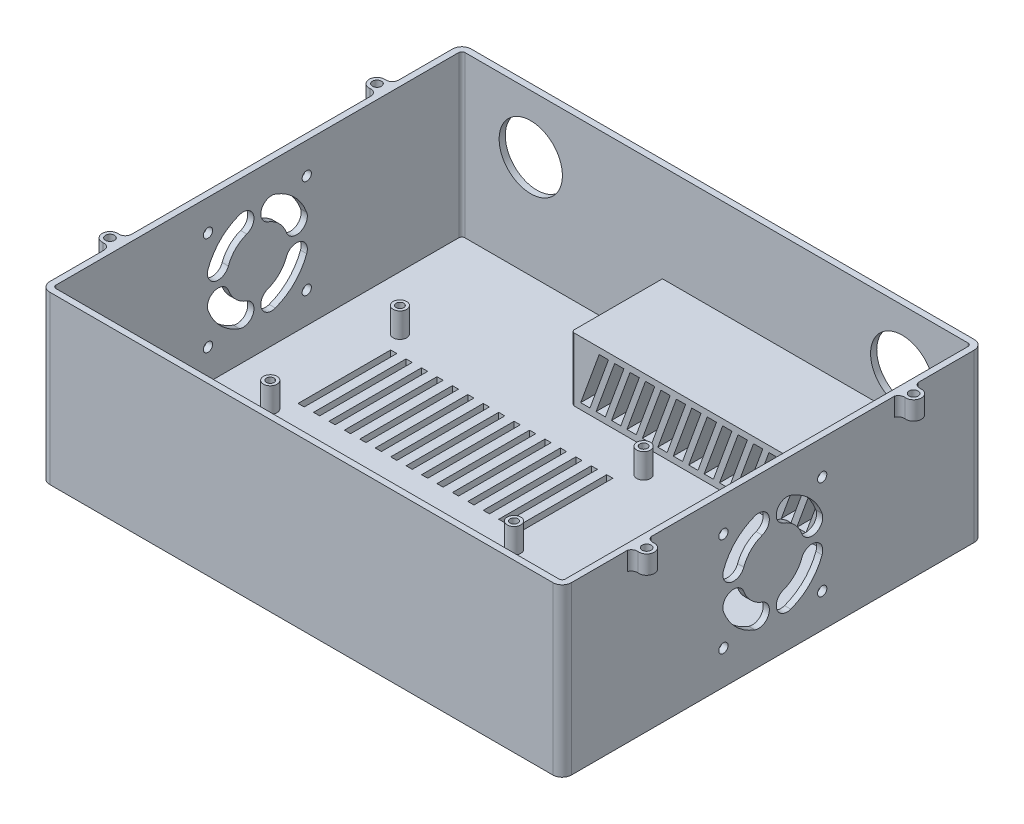
SolidWorks part; units mm, degrees
ref_plane "前视基准面" through (0, 0, 0) normal (0, 0, 1) x (1, 0, 0)
ref_plane "上视基准面" through (0, 0, 0) normal (0, 1, 0) x (1, 0, 0)
ref_plane "右视基准面" through (0, 0, 0) normal (1, 0, 0) x (0, 0, -1)
sketch "草图2" plane through (0, 0, 0) normal (0, 1, 0) x (1, 0, 0)
  line L0 (-81.5, -68.25) -> (81.5, -68.25)
  line L1 (-81.5, -66.25) -> (81.5, -66.25)
  line L2 (-82.5, -65.25) -> (-82.5, 65.25)
  line L3 (-81.5, 66.25) -> (81.5, 66.25)
  line L4 (82.5, -65.25) -> (82.5, 65.25)
  line L5 (-82.5, -66.25) -> (82.5, 66.25) construction
  line L6 (-82.5, 66.25) -> (82.5, -66.25) construction
  line L7 (84.5, -65.25) -> (84.5, 65.25)
  line L8 (-81.5, 68.25) -> (81.5, 68.25)
  line L9 (-84.5, -65.25) -> (-84.5, 65.25)
  arc A0 (-81.5, -66.25) -> (-82.5, -65.25) centre (-81.5, -65.25) cw
  arc A1 (81.5, -66.25) -> (82.5, -65.25) centre (81.5, -65.25) ccw
  arc A2 (81.5, 66.25) -> (82.5, 65.25) centre (81.5, 65.25) cw
  arc A3 (-82.5, 65.25) -> (-81.5, 66.25) centre (-81.5, 65.25) cw
  arc A4 (81.5, -68.25) -> (84.5, -65.25) centre (81.5, -65.25) ccw
  arc A5 (81.5, 68.25) -> (84.5, 65.25) centre (81.5, 65.25) cw
  arc A6 (-84.5, 65.25) -> (-81.5, 68.25) centre (-81.5, 65.25) cw
  arc A7 (-81.5, -68.25) -> (-84.5, -65.25) centre (-81.5, -65.25) cw
  point P0 (0, 0)
  dimension "D3" = 1
  dimension "D1" = 132.5
  dimension "D2" = 165
  dimension "D4" = 2
extrude "凸台-拉伸4" add sketch "草图2" along normal blind 52
sketch "草图6" plane through (0, 0, 0) normal (0, -1, 0) x (-1, 0, 0)
  line L0 (-84.5, -65.25) -> (-84.5, 65.25) construction
  line L1 (81.5, -68.25) -> (-81.5, -68.25)
  line L2 (84.5, -65.25) -> (84.5, 65.25)
  line L3 (81.5, 68.25) -> (-81.5, 68.25)
  line L4 (-84.5, -65.25) -> (-84.5, 65.25)
  line L5 (-81.5, 68.25) -> (81.5, 68.25) construction
  line L6 (84.5, 65.25) -> (84.5, -65.25) construction
  line L7 (81.5, -68.25) -> (-81.5, -68.25) construction
  arc A0 (84.5, 65.25) -> (81.5, 68.25) centre (81.5, 65.25) ccw
  arc A1 (-81.5, 68.25) -> (-84.5, 65.25) centre (-81.5, 65.25) ccw
  arc A2 (-81.5, -68.25) -> (-84.5, -65.25) centre (-81.5, -65.25) cw
  arc A3 (81.5, -68.25) -> (84.5, -65.25) centre (81.5, -65.25) ccw
  dimension "D1" = 3
extrude "凸台-拉伸5" add sketch "草图6" along normal blind 2
sketch "草图7" plane through (0, 0, 0) normal (0, 1, 0) x (1, 0, 0)
  line L0 (82.5, -65.25) -> (82.5, 65.25) construction
  line L1 (-17.5, 66.25) -> (82.5, 66.25)
  line L2 (-17.5, 66.25) -> (-17.5, 37.75)
  line L3 (-16.5, 36.75) -> (82.5, 36.75)
  line L4 (82.5, 66.25) -> (82.5, 36.75)
  line L5 (81.5, 66.25) -> (-81.5, 66.25) construction
  arc A0 (-17.5, 37.75) -> (-16.5, 36.75) centre (-16.5, 37.75) ccw
  dimension "D1" = 1
  dimension "D2" = 29.5
  dimension "D3" = 100
extrude "凸台-拉伸6" add sketch "草图7" along normal blind 20.5
sketch "草图14" plane through (0, 0, -68.25) normal (0, 0, -1) x (-1, 0, 0)
  line L0 (0, 68.0552) -> (0, -20.1573) construction
  line L1 (-81.5, 52) -> (81.5, 52) construction
  circle A0 centre (-60.175, 33.275) radius 10.25
  circle A1 centre (60.175, 33.275) radius 10.25
  dimension "D1" = 20.5
  dimension "D2" = 120.35
  dimension "D3" = 18.725
extrude "切除-拉伸2" cut sketch "草图14" against normal blind 2
sketch "草图20" plane through (0, 0, -36.75) normal (0, 0, 1) x (1, 0, 0)
  line L0 (-14.5, 2) -> (-8.4945, 18.5)
  line L1 (-14.5, 2) -> (-11.5, 2)
  line L2 (-8.4945, 18.5) -> (-5.4945, 18.5)
  line L3 (-11.5, 2) -> (-5.4945, 18.5)
  line L4 (-16.5, 0) -> (82.5, 0) construction
  line L5 (-16.5, 20.5) -> (-16.5, 0) construction
  line L6 (-16.5, 20.5) -> (82.5, 20.5) construction
  line L7 (-9.5, 2) -> (-3.4945, 18.5)
  line L8 (-3.4945, 18.5) -> (-0.4945, 18.5)
  line L9 (-6.5, 2) -> (-0.4945, 18.5)
  line L10 (-9.5, 2) -> (-6.5, 2)
  line L11 (-4.5, 2) -> (1.5055, 18.5)
  line L12 (1.5055, 18.5) -> (4.5055, 18.5)
  line L13 (-1.5, 2) -> (4.5055, 18.5)
  line L14 (-4.5, 2) -> (-1.5, 2)
  line L15 (0.5, 2) -> (6.5055, 18.5)
  line L16 (6.5055, 18.5) -> (9.5055, 18.5)
  line L17 (3.5, 2) -> (9.5055, 18.5)
  line L18 (0.5, 2) -> (3.5, 2)
  line L19 (5.5, 2) -> (11.5055, 18.5)
  line L20 (11.5055, 18.5) -> (14.5055, 18.5)
  line L21 (8.5, 2) -> (14.5055, 18.5)
  line L22 (5.5, 2) -> (8.5, 2)
  line L23 (10.5, 2) -> (16.5055, 18.5)
  line L24 (16.5055, 18.5) -> (19.5055, 18.5)
  line L25 (13.5, 2) -> (19.5055, 18.5)
  line L26 (10.5, 2) -> (13.5, 2)
  line L27 (15.5, 2) -> (21.5055, 18.5)
  line L28 (21.5055, 18.5) -> (24.5055, 18.5)
  line L29 (18.5, 2) -> (24.5055, 18.5)
  line L30 (15.5, 2) -> (18.5, 2)
  line L31 (20.5, 2) -> (26.5055, 18.5)
  line L32 (26.5055, 18.5) -> (29.5055, 18.5)
  line L33 (23.5, 2) -> (29.5055, 18.5)
  line L34 (20.5, 2) -> (23.5, 2)
  line L35 (25.5, 2) -> (31.5055, 18.5)
  line L36 (31.5055, 18.5) -> (34.5055, 18.5)
  line L37 (28.5, 2) -> (34.5055, 18.5)
  line L38 (25.5, 2) -> (28.5, 2)
  line L39 (30.5, 2) -> (36.5055, 18.5)
  line L40 (36.5055, 18.5) -> (39.5055, 18.5)
  line L41 (33.5, 2) -> (39.5055, 18.5)
  line L42 (30.5, 2) -> (33.5, 2)
  line L43 (35.5, 2) -> (41.5055, 18.5)
  line L44 (41.5055, 18.5) -> (44.5055, 18.5)
  line L45 (38.5, 2) -> (44.5055, 18.5)
  line L46 (35.5, 2) -> (38.5, 2)
  line L47 (40.5, 2) -> (46.5055, 18.5)
  line L48 (46.5055, 18.5) -> (49.5055, 18.5)
  line L49 (43.5, 2) -> (49.5055, 18.5)
  line L50 (40.5, 2) -> (43.5, 2)
  line L51 (45.5, 2) -> (51.5055, 18.5)
  line L52 (51.5055, 18.5) -> (54.5055, 18.5)
  line L53 (48.5, 2) -> (54.5055, 18.5)
  line L54 (45.5, 2) -> (48.5, 2)
  line L55 (50.5, 2) -> (56.5055, 18.5)
  line L56 (56.5055, 18.5) -> (59.5055, 18.5)
  line L57 (53.5, 2) -> (59.5055, 18.5)
  line L58 (50.5, 2) -> (53.5, 2)
  line L59 (55.5, 2) -> (61.5055, 18.5)
  line L60 (61.5055, 18.5) -> (64.5055, 18.5)
  line L61 (58.5, 2) -> (64.5055, 18.5)
  line L62 (55.5, 2) -> (58.5, 2)
  line L63 (60.5, 2) -> (66.5055, 18.5)
  line L64 (66.5055, 18.5) -> (69.5055, 18.5)
  line L65 (63.5, 2) -> (69.5055, 18.5)
  line L66 (60.5, 2) -> (63.5, 2)
  line L67 (65.5, 2) -> (71.5055, 18.5)
  line L68 (71.5055, 18.5) -> (74.5055, 18.5)
  line L69 (68.5, 2) -> (74.5055, 18.5)
  line L70 (65.5, 2) -> (68.5, 2)
  line L71 (70.5, 2) -> (76.5055, 18.5)
  line L72 (76.5055, 18.5) -> (79.5055, 18.5)
  line L73 (73.5, 2) -> (79.5055, 18.5)
  line L74 (70.5, 2) -> (73.5, 2)
  line L75 (-14.5, 2) -> (-9.5, 2) construction
  dimension "D1" = 2
  dimension "D2" = 2
  dimension "D3" = 2
  dimension "D4" = 110
  dimension "D5" = 3
  dimension "D7" = 5
  dimension "D6" = 18
sketch "草图21" plane through (0, 0, -36.75) normal (0, 0, 1) x (1, 0, 0)
extrude "切除-拉伸4" cut sketch "草图20" against normal blind 35
sketch "草图22" plane through (0, 0, -68.25) normal (0, 0, -1) x (-1, 0, 0)
  line L1 (81.5, -2) -> (-81.5, -2) construction
  text T0 "<b>GAAS</b>" font "Monospac821 BT" height 16.5
  dimension "D1" = 4
  dimension "D2" = 4
extrude "切除-拉伸5" cut sketch "草图22" against normal blind 0.05
sketch "草图25" plane through (0, 0, 0) normal (0, 1, 0) x (1, 0, 0)
  line L0 (-81.5, -66.25) -> (81.5, -66.25) construction
  line L1 (0, 72.7206) -> (0, -77.048) construction
  circle A0 centre (-60.15, -50.45) radius 10.15
  circle A1 centre (60.15, -50.45) radius 10.15
  dimension "D2" = 20.3
  dimension "D3" = 15.8
  dimension "D1" = 120.3
extrude "切除-拉伸6" cut sketch "草图25" against normal blind 2
sketch "草图26" plane through (0, 0, 0) normal (0, 1, 0) x (1, 0, 0)
  line L0 (-104.0478, -34.75) -> (111.3857, -35.8789) construction
  line L1 (-81.5, -66.25) -> (81.5, -66.25) construction
  line L3 (-16.5, 36.75) -> (82.5, 36.75) construction
  line L10 (-82.5, 65.25) -> (-82.5, -65.25) construction
  circle A0 centre (13.9, 28.75) radius 1.25
  circle A1 centre (13.9, -13.25) radius 1.25
  circle A2 centre (-65.065, -13.25) radius 1.25
  circle A3 centre (-65.065, 28.75) radius 1.25
  circle A4 centre (13.9, 28.75) radius 2.2
  circle A5 centre (13.9, -13.25) radius 2.2
  circle A6 centre (-65.065, -13.25) radius 2.2
  circle A7 centre (-65.065, 28.75) radius 2.2
  dimension "D7" = 8
  dimension "D9" = 2.5
  dimension "D4" = 4.4
  dimension "D1" = 31.5
  dimension "D2" = 71.9578
  dimension "D3" = 96.4
  dimension "D11" = 42
  dimension "D12" = 78.965
extrude "凸台-拉伸13" add sketch "草图26" along normal blind 8
sketch "草图30" plane through (0, 0, 0) normal (0, 1, 0) x (1, 0, 0)
  line L0 (-65.065, 28.75) -> (-65.065, -13.25) construction
  line L1 (-62.065, 22.75) -> (-60.065, 22.75)
  line L2 (-62.065, 22.75) -> (-62.065, -7.25)
  line L3 (-62.065, -7.25) -> (-60.065, -7.25)
  line L4 (-60.065, 22.75) -> (-60.065, -7.25)
  line L5 (-57.065, 22.75) -> (-55.065, 22.75)
  line L6 (-57.065, 22.75) -> (-57.065, -7.25)
  line L7 (-55.065, 22.75) -> (-55.065, -7.25)
  line L8 (-57.065, -7.25) -> (-55.065, -7.25)
  line L9 (-52.065, 22.75) -> (-50.065, 22.75)
  line L10 (-52.065, 22.75) -> (-52.065, -7.25)
  line L11 (-50.065, 22.75) -> (-50.065, -7.25)
  line L12 (-52.065, -7.25) -> (-50.065, -7.25)
  line L13 (-47.065, 22.75) -> (-45.065, 22.75)
  line L14 (-47.065, 22.75) -> (-47.065, -7.25)
  line L15 (-45.065, 22.75) -> (-45.065, -7.25)
  line L16 (-47.065, -7.25) -> (-45.065, -7.25)
  line L17 (-42.065, 22.75) -> (-40.065, 22.75)
  line L18 (-42.065, 22.75) -> (-42.065, -7.25)
  line L19 (-40.065, 22.75) -> (-40.065, -7.25)
  line L20 (-42.065, -7.25) -> (-40.065, -7.25)
  line L21 (-37.065, 22.75) -> (-35.065, 22.75)
  line L22 (-37.065, 22.75) -> (-37.065, -7.25)
  line L23 (-35.065, 22.75) -> (-35.065, -7.25)
  line L24 (-37.065, -7.25) -> (-35.065, -7.25)
  line L25 (-32.065, 22.75) -> (-30.065, 22.75)
  line L26 (-32.065, 22.75) -> (-32.065, -7.25)
  line L27 (-30.065, 22.75) -> (-30.065, -7.25)
  line L28 (-32.065, -7.25) -> (-30.065, -7.25)
  line L29 (-27.065, 22.75) -> (-25.065, 22.75)
  line L30 (-27.065, 22.75) -> (-27.065, -7.25)
  line L31 (-25.065, 22.75) -> (-25.065, -7.25)
  line L32 (-27.065, -7.25) -> (-25.065, -7.25)
  line L33 (-22.065, 22.75) -> (-20.065, 22.75)
  line L34 (-22.065, 22.75) -> (-22.065, -7.25)
  line L35 (-20.065, 22.75) -> (-20.065, -7.25)
  line L36 (-22.065, -7.25) -> (-20.065, -7.25)
  line L37 (-17.065, 22.75) -> (-15.065, 22.75)
  line L38 (-17.065, 22.75) -> (-17.065, -7.25)
  line L39 (-15.065, 22.75) -> (-15.065, -7.25)
  line L40 (-17.065, -7.25) -> (-15.065, -7.25)
  line L41 (-12.065, 22.75) -> (-10.065, 22.75)
  line L42 (-12.065, 22.75) -> (-12.065, -7.25)
  line L43 (-10.065, 22.75) -> (-10.065, -7.25)
  line L44 (-12.065, -7.25) -> (-10.065, -7.25)
  line L45 (-7.065, 22.75) -> (-5.065, 22.75)
  line L46 (-7.065, 22.75) -> (-7.065, -7.25)
  line L47 (-5.065, 22.75) -> (-5.065, -7.25)
  line L48 (-7.065, -7.25) -> (-5.065, -7.25)
  line L49 (-2.065, 22.75) -> (-0.065, 22.75)
  line L50 (-2.065, 22.75) -> (-2.065, -7.25)
  line L51 (-0.065, 22.75) -> (-0.065, -7.25)
  line L52 (-2.065, -7.25) -> (-0.065, -7.25)
  line L53 (2.935, 22.75) -> (4.935, 22.75)
  line L54 (2.935, 22.75) -> (2.935, -7.25)
  line L55 (4.935, 22.75) -> (4.935, -7.25)
  line L56 (2.935, -7.25) -> (4.935, -7.25)
  line L57 (7.935, 22.75) -> (9.935, 22.75)
  line L58 (7.935, 22.75) -> (7.935, -7.25)
  line L59 (9.935, 22.75) -> (9.935, -7.25)
  line L60 (7.935, -7.25) -> (9.935, -7.25)
  line L61 (-62.065, 22.75) -> (-57.065, 22.75) construction
  dimension "D1" = 2
  dimension "D2" = 30
  dimension "D3" = 3
  dimension "D4" = 6
  dimension "D5" = 15
  dimension "D6" = 5
extrude "切除-拉伸8" cut sketch "草图30" against normal blind 8
sketch "草图31" plane through (84.5, 0, 0) normal (1, 0, 0) x (0, 0, -1)
  line L0 (0, 60.1116) -> (0, -13.4556) construction
  line L1 (-16, 41) -> (16, 41) construction
  line L2 (-16, 41) -> (-16, 9) construction
  line L3 (-16, 9) -> (16, 9) construction
  line L4 (16, 41) -> (16, 9) construction
  line L5 (-25.1333, 25) -> (23.8315, 25) construction
  line L6 (0, 25) -> (-7.4218, 45.3911) construction
  line L7 (65.25, -2) -> (-65.25, -2) construction
  line L8 (0, 25) -> (-23.8658, 33.6865) construction
  circle A0 centre (-16, 41) radius 1.5
  circle A1 centre (16, 41) radius 1.5
  circle A2 centre (16, 9) radius 1.5
  circle A3 centre (-16, 9) radius 1.5
  arc A4 (-4.6173, 37.6859) -> (-12.6859, 29.6173) centre (0, 25) ccw construction
  arc A5 (-5.8143, 40.9748) -> (-15.9748, 30.8143) centre (0, 25) ccw
  arc A6 (-3.4202, 34.3969) -> (-9.3969, 28.4202) centre (0, 25) ccw
  arc A7 (-3.4202, 34.3969) -> (-5.8143, 40.9748) centre (-4.6173, 37.6859) ccw
  arc A8 (-15.9748, 30.8143) -> (-9.3969, 28.4202) centre (-12.6859, 29.6173) ccw
  arc A9 (12.6859, 29.6173) -> (4.6173, 37.6859) centre (0, 25) ccw construction
  arc A10 (15.9748, 30.8143) -> (5.8143, 40.9748) centre (0, 25) ccw
  arc A11 (9.3969, 28.4202) -> (3.4202, 34.3969) centre (0, 25) ccw
  arc A12 (9.3969, 28.4202) -> (15.9748, 30.8143) centre (12.6859, 29.6173) ccw
  arc A13 (5.8143, 40.9748) -> (3.4202, 34.3969) centre (4.6173, 37.6859) ccw
  arc A14 (4.6173, 12.3141) -> (12.6859, 20.3827) centre (0, 25) ccw construction
  arc A15 (5.8143, 9.0252) -> (15.9748, 19.1857) centre (0, 25) ccw
  arc A16 (3.4202, 15.6031) -> (9.3969, 21.5798) centre (0, 25) ccw
  arc A17 (3.4202, 15.6031) -> (5.8143, 9.0252) centre (4.6173, 12.3141) ccw
  arc A18 (15.9748, 19.1857) -> (9.3969, 21.5798) centre (12.6859, 20.3827) ccw
  arc A19 (-12.6859, 20.3827) -> (-4.6173, 12.3141) centre (0, 25) ccw construction
  arc A20 (-15.9748, 19.1857) -> (-5.8143, 9.0252) centre (0, 25) ccw
  arc A21 (-9.3969, 21.5798) -> (-3.4202, 15.6031) centre (0, 25) ccw
  arc A22 (-9.3969, 21.5798) -> (-15.9748, 19.1857) centre (-12.6859, 20.3827) ccw
  arc A23 (-5.8143, 9.0252) -> (-3.4202, 15.6031) centre (-4.6173, 12.3141) ccw
  point P15 (16, 25)
  point P19 (-9.5459, 34.5459)
  point P32 (9.5459, 34.5459)
  point P39 (9.5459, 15.4541)
  point P46 (-9.5459, 15.4541)
  point P51 (0, 25)
  dimension "D3" = 3
  dimension "D4" = 10
  dimension "D5" = 17
  dimension "D1" = 32
  dimension "D2" = 11
  dimension "D6" = 20
  dimension "D7" = 20
  dimension "D8" = 4
extrude "切除-拉伸11" cut sketch "草图31" against normal blind 8
sketch "草图35" plane through (-84.5, 0, 0) normal (-1, 0, 0) x (0, 0, 1)
  line L0 (0, 74.5115) -> (0, -18.3088) construction
  line L2 (-76.8975, 26) -> (79.9658, 26) construction
  line L3 (-65.25, 52) -> (65.25, 52) construction
  line L4 (0, 26) -> (-9.2345, 51.3717) construction
  line L5 (-16, 42) -> (16, 42) construction
  line L6 (-16, 42) -> (-16, 10) construction
  line L7 (-16, 10) -> (16, 10) construction
  line L8 (16, 42) -> (16, 10) construction
  line L9 (0, 26) -> (-23.8332, 34.6746) construction
  circle A0 centre (-16, 42) radius 1.5
  circle A1 centre (16, 42) radius 1.5
  circle A2 centre (16, 10) radius 1.5
  circle A3 centre (-16, 10) radius 1.5
  arc A4 (-4.6173, 38.6859) -> (-12.6859, 30.6173) centre (0, 26) ccw construction
  arc A5 (-5.8143, 41.9748) -> (-15.9748, 31.8143) centre (0, 26) ccw
  arc A6 (-3.4202, 35.3969) -> (-9.3969, 29.4202) centre (0, 26) ccw
  arc A7 (-3.4202, 35.3969) -> (-5.8143, 41.9748) centre (-4.6173, 38.6859) ccw
  arc A8 (-15.9748, 31.8143) -> (-9.3969, 29.4202) centre (-12.6859, 30.6173) ccw
  arc A9 (12.6859, 30.6173) -> (4.6173, 38.6859) centre (0, 26) ccw construction
  arc A10 (15.9748, 31.8143) -> (5.8143, 41.9748) centre (0, 26) ccw
  arc A11 (9.3969, 29.4202) -> (3.4202, 35.3969) centre (0, 26) ccw
  arc A12 (9.3969, 29.4202) -> (15.9748, 31.8143) centre (12.6859, 30.6173) ccw
  arc A13 (5.8143, 41.9748) -> (3.4202, 35.3969) centre (4.6173, 38.6859) ccw
  arc A14 (4.6173, 13.3141) -> (12.6859, 21.3827) centre (0, 26) ccw construction
  arc A15 (5.8143, 10.0252) -> (15.9748, 20.1857) centre (0, 26) ccw
  arc A16 (3.4202, 16.6031) -> (9.3969, 22.5798) centre (0, 26) ccw
  arc A17 (3.4202, 16.6031) -> (5.8143, 10.0252) centre (4.6173, 13.3141) ccw
  arc A18 (15.9748, 20.1857) -> (9.3969, 22.5798) centre (12.6859, 21.3827) ccw
  arc A19 (-12.6859, 21.3827) -> (-4.6173, 13.3141) centre (0, 26) ccw construction
  arc A20 (-15.9748, 20.1857) -> (-5.8143, 10.0252) centre (0, 26) ccw
  arc A21 (-9.3969, 22.5798) -> (-3.4202, 16.6031) centre (0, 26) ccw
  arc A22 (-9.3969, 22.5798) -> (-15.9748, 20.1857) centre (-12.6859, 21.3827) ccw
  arc A23 (-5.8143, 10.0252) -> (-3.4202, 16.6031) centre (-4.6173, 13.3141) ccw
  point P20 (-9.5459, 35.5459)
  point P30 (9.5459, 35.5459)
  point P37 (9.5459, 16.4541)
  point P44 (-9.5459, 16.4541)
  point P49 (0, 26)
  dimension "D3" = 3
  dimension "D6" = 10
  dimension "D7" = 17
  dimension "D8" = 4
  dimension "D1" = 26
  dimension "D2" = 32
  dimension "D4" = 20
  dimension "D5" = 20
extrude "切除-拉伸12" cut sketch "草图35" against normal blind 8
sketch "草图37" plane through (0, 52, 0) normal (0, 1, 0) x (1, 0, 0)
  line L0 (-84.5, 65.25) -> (-84.5, -65.25) construction
  line L1 (81.5, 68.25) -> (-81.5, 68.25) construction
  line L2 (-84.5, 47.7221) -> (-84.5, 38.7779)
  line L4 (-17.065, 0) -> (29.4113, 0) construction
  line L5 (-17.065, 22.75) -> (-17.065, -7.25) construction
  line L6 (-0.065, 20.2233) -> (-0.065, -25.2268) construction
  line L7 (-0.065, -7.25) -> (-0.065, 22.75) construction
  line L8 (84.37, 47.7221) -> (84.37, 38.7779)
  line L9 (84.37, -47.7221) -> (84.37, -38.7779)
  line L10 (-84.5, -47.7221) -> (-84.5, -38.7779)
  arc A0 (-86.7222, 45.7345) -> (-86.7222, 40.7655) centre (-87, 43.25) ccw
  arc A1 (-84.5, 38.7779) -> (-86.7222, 40.7655) centre (-86.5, 38.7779) ccw
  arc A2 (-86.7222, 45.7345) -> (-84.5, 47.7221) centre (-86.5, 47.7221) ccw
  circle A3 centre (-87, 43.25) radius 1.45
  circle A4 centre (86.87, 43.25) radius 1.45
  arc A5 (86.5922, 45.7345) -> (84.37, 47.7221) centre (86.37, 47.7221) cw
  arc A6 (84.37, 38.7779) -> (86.5922, 40.7655) centre (86.37, 38.7779) cw
  arc A7 (86.5922, 45.7345) -> (86.5922, 40.7655) centre (86.87, 43.25) cw
  arc A8 (86.5922, -45.7345) -> (86.5922, -40.7655) centre (86.87, -43.25) ccw
  arc A9 (84.37, -38.7779) -> (86.5922, -40.7655) centre (86.37, -38.7779) ccw
  arc A10 (86.5922, -45.7345) -> (84.37, -47.7221) centre (86.37, -47.7221) ccw
  circle A11 centre (86.87, -43.25) radius 1.45
  circle A12 centre (-87, -43.25) radius 1.45
  arc A13 (-86.7222, -45.7345) -> (-84.5, -47.7221) centre (-86.5, -47.7221) cw
  arc A14 (-84.5, -38.7779) -> (-86.7222, -40.7655) centre (-86.5, -38.7779) cw
  arc A15 (-86.7222, -45.7345) -> (-86.7222, -40.7655) centre (-87, -43.25) cw
  dimension "D1" = 5
  dimension "D2" = 4
  dimension "D3" = 25
  dimension "D4" = 2.9
extrude "凸台-拉伸14" add sketch "草图37" against normal blind 6
